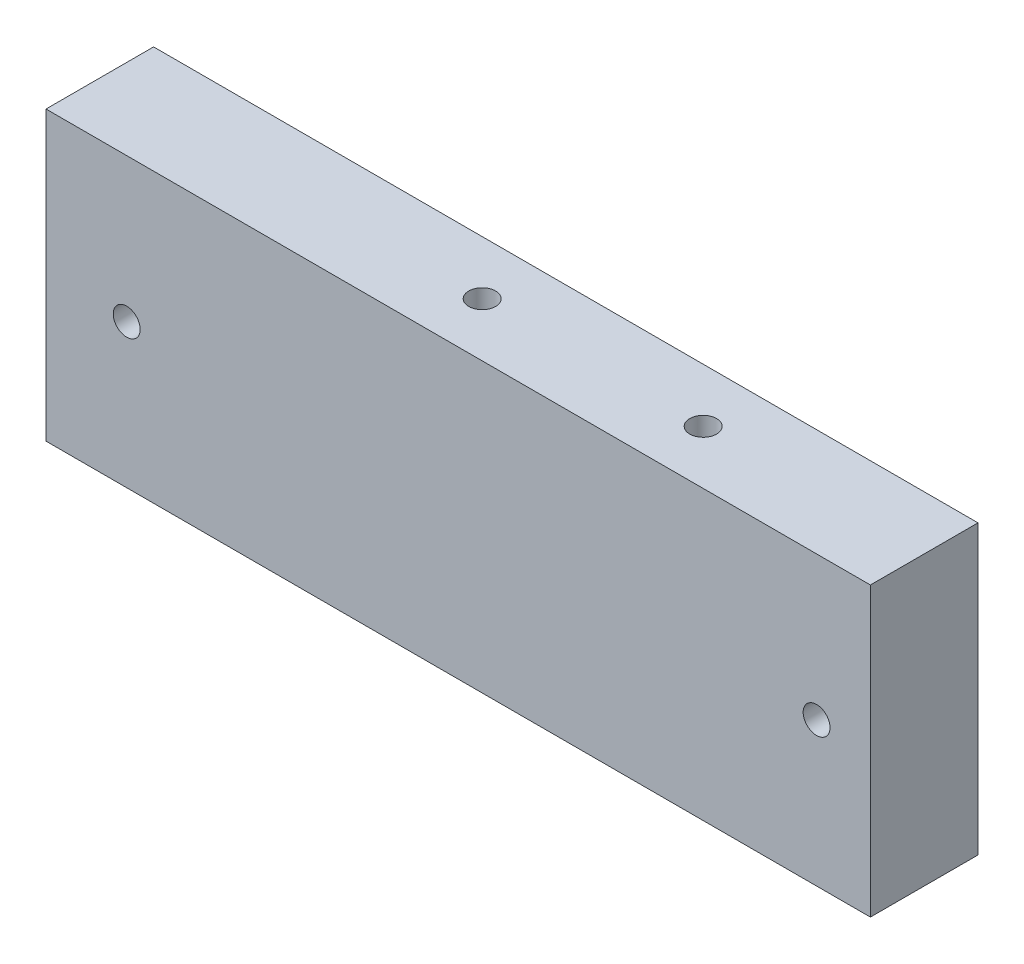
SolidWorks part; units mm, degrees
material "Beech"
ref_plane "Front Plane" through (0, 0, 0) normal (0, 0, 1) x (1, 0, 0)
ref_plane "Top Plane" through (0, 0, 0) normal (0, 1, 0) x (1, 0, 0)
ref_plane "Right Plane" through (0, 0, 0) normal (1, 0, 0) x (0, 0, -1)
sketch "Sketch1" plane through (0, 0, 0) normal (0, 0, 1) x (1, 0, 0)
  line L0 (-244.0045, -53) -> (-244.0045, -19) construction
  line L1 (-341.3045, -19.05) -> (-244.0045, -19.05)
  line L2 (-341.3045, -19.05) -> (-341.3045, -53)
  line L3 (-341.3045, -53) -> (-244.0045, -53)
  line L4 (-244.0045, -19.05) -> (-244.0045, -53)
  dimension "D2" = 33.95
extrude "Boss-Extrude1" add sketch "Sketch1" against normal blind 12.7
hole_wizard "Hole1" positions "Sketch2" profile "Sketch3" legacy
sketch "Sketch2" plane through (-124.0045, 0, -10.4243) normal (0, 1, 0) x (-1, 0, 0)
  line L21 (0, 109.0243) -> (0, 155.0243) construction
  point P37 (126.35, 161.3743)
  point P42 (146.0833, 4.0743)
  point P44 (172.1667, 4.0743)
  point P63 (126.35, 34.5243)
  point P65 (126.35, 130.9243)
  point P76 (-172.1667, 4.0743)
  point P77 (-146.0833, 4.0743)
  point P78 (-126.35, 34.5243)
  point P79 (-126.35, 130.9243)
  point P80 (-126.35, 161.3743)
sketch "Sketch3" plane through (-250.3545, 0, 150.95) normal (1, 0, 0) x (0, 0, 1)
  line L0 (0, 0) -> (0, 32.7039)
  line L1 (0, 32.7039) -> (1.5875, 31.75)
  line L2 (1.5875, 31.75) -> (1.5875, 4.0177)
  line L3 (1.5875, 4.0177) -> (5.08, 0)
  line L4 (5.08, 0) -> (0, 0)
  line L5 (0, -14.3089) -> (0, 102.4216) construction
  line L6 (0, 32.7039) -> (-1.5875, 31.75) construction
  line L7 (-1.5875, 4.0177) -> (-5.08, 0) construction
  dimension "Diameter" = 3.175
  dimension "Depth" = 31.75
  dimension "C-Sink Diameter" = 10.16
  dimension "C-Sink Angle" = 82
  dimension "Drill Angle" = 118
hole_wizard "Hole2" positions "Sketch4" profile "Sketch5" legacy
sketch "Sketch4" plane through (-124.0045, -72.05, -10.4243) normal (0, -1, 0) x (1, 0, 0)
  line L21 (0, 109.0243) -> (0, 155.0243) construction
  point P37 (126.35, 161.3743)
  point P42 (146.0833, 4.0743)
  point P44 (172.1667, 4.0743)
  point P63 (126.35, 34.5243)
  point P65 (126.35, 130.9243)
  point P76 (-172.1667, 4.0743)
  point P77 (-146.0833, 4.0743)
  point P78 (-126.35, 34.5243)
  point P79 (-126.35, 130.9243)
  point P80 (-126.35, 161.3743)
sketch "Sketch5" plane through (2.3455, -72.05, 150.95) normal (1, 0, 0) x (0, 0, -1)
  line L0 (0, 0) -> (0, 32.7039)
  line L1 (0, 32.7039) -> (1.5875, 31.75)
  line L2 (1.5875, 31.75) -> (1.5875, 4.0177)
  line L3 (1.5875, 4.0177) -> (5.08, 0)
  line L4 (5.08, 0) -> (0, 0)
  line L5 (0, -14.3089) -> (0, 102.4216) construction
  line L6 (0, 32.7039) -> (-1.5875, 31.75) construction
  line L7 (-1.5875, 4.0177) -> (-5.08, 0) construction
  dimension "Diameter" = 3.175
  dimension "Depth" = 31.75
  dimension "C-Sink Diameter" = 10.16
  dimension "C-Sink Angle" = 82
  dimension "Drill Angle" = 118
hole_wizard "Hole5" positions "Sketch8" profile "Sketch9" legacy
sketch "Sketch8" plane through (-124.0045, -208.2867, -12.7) normal (0, 0, -1) x (-1, 0, 0)
  line L0 (120, 172.2617) -> (217.3, 172.2617) construction
  point P8 (126.35, 172.2617)
  point P10 (207.775, 172.2617)
sketch "Sketch9" plane through (-331.7795, -36.025, -12.7) normal (1, 0, 0) x (0, 1, 0)
  line L0 (0, 0) -> (0, 32.7039)
  line L1 (0, 32.7039) -> (1.5875, 31.75)
  line L2 (1.5875, 31.75) -> (1.5875, 4.0177)
  line L3 (1.5875, 4.0177) -> (5.08, 0)
  line L4 (5.08, 0) -> (0, 0)
  line L5 (0, -14.3089) -> (0, 102.4216) construction
  line L6 (0, 32.7039) -> (-1.5875, 31.75) construction
  line L7 (-1.5875, 4.0177) -> (-5.08, 0) construction
  dimension "Diameter" = 3.175
  dimension "Depth" = 31.75
  dimension "C-Sink Diameter" = 10.16
  dimension "C-Sink Angle" = 82
  dimension "Drill Angle" = 118
hole_wizard "Hole6" positions "Sketch10" profile "Sketch11" legacy
sketch "Sketch10" plane through (-124.0045, -6.35, -10.4243) normal (0, 1, 0) x (-1, 0, 0)
  line L12 (0, 0) -> (0, 155.0243) construction
  point P0 (-207.775, 333.0214)
  point P3 (-207.775, 225.489)
  point P6 (-207.775, 137.4243)
  point P9 (-172.1667, 4.0743)
  point P12 (-146.0833, 4.0743)
  point P15 (-94.6, 161.3743)
  point P21 (94.6, 161.3743)
  point P24 (146.0833, 4.0743)
  point P27 (172.1667, 4.0743)
  point P30 (207.775, 137.4243)
  point P33 (207.775, 225.489)
  point P36 (207.775, 333.0214)
  point P39 (166.7958, 301.9704)
  point P42 (40.9792, 301.9704)
  point P45 (-40.9792, 301.9704)
  point P48 (-166.7958, 301.9704)
  point P51 (0, 193.1243)
  point P54 (0, 301.9704)
  point P57 (0, 412.3664)
  point P80 (-126.35, 106.8243)
  point P82 (-126.35, 58.6243)
  point P96 (126.35, 58.6243)
  point P97 (126.35, 106.8243)
sketch "Sketch11" plane through (83.7705, -6.35, 322.5971) normal (1, 0, 0) x (0, 0, 1)
  line L0 (0, 0) -> (0, 32.7039)
  line L1 (0, 32.7039) -> (1.5875, 31.75)
  line L2 (1.5875, 31.75) -> (1.5875, 4.0177)
  line L3 (1.5875, 4.0177) -> (5.08, 0)
  line L4 (5.08, 0) -> (0, 0)
  line L5 (0, -14.3089) -> (0, 102.4216) construction
  line L6 (0, 32.7039) -> (-1.5875, 31.75) construction
  line L7 (-1.5875, 4.0177) -> (-5.08, 0) construction
  dimension "Diameter" = 3.175
  dimension "Depth" = 31.75
  dimension "C-Sink Diameter" = 10.16
  dimension "C-Sink Angle" = 82
  dimension "Drill Angle" = 118
